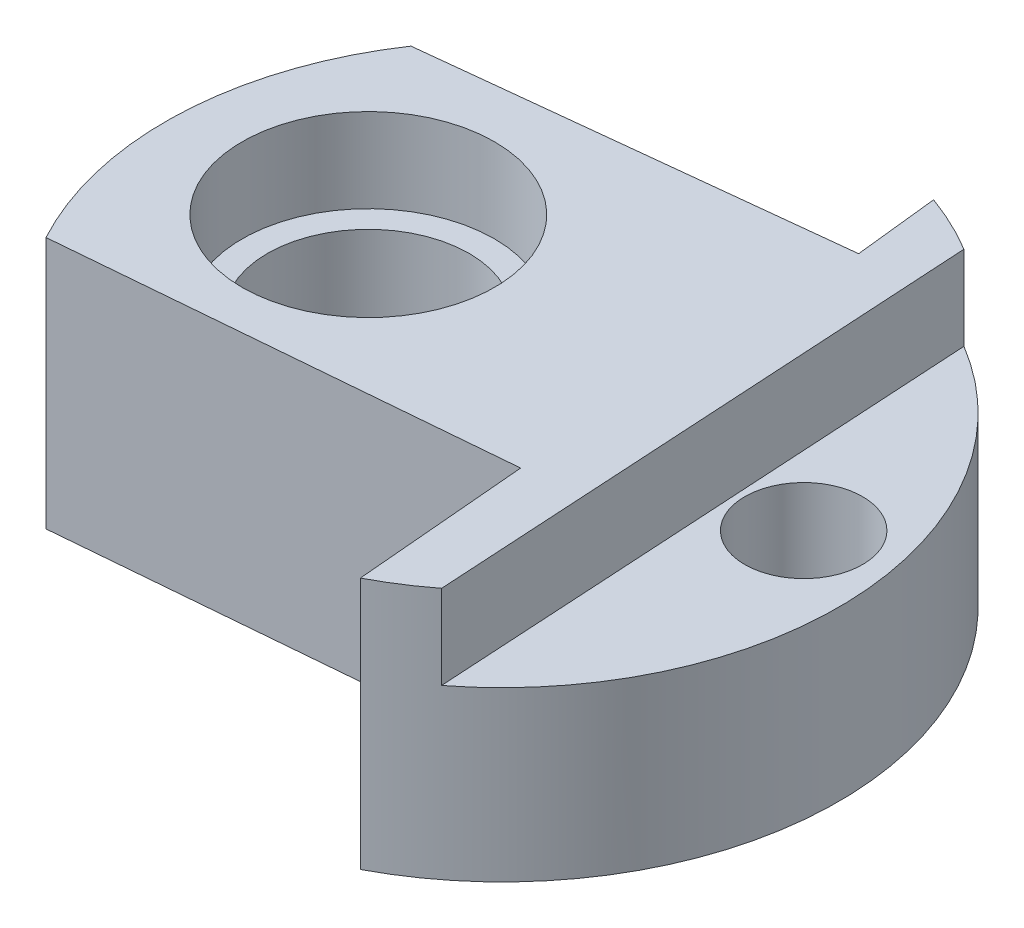
SolidWorks part; units mm, degrees
ref_plane "Front Plane" through (0, 0, 0) normal (0, 0, 1) x (1, 0, 0)
ref_plane "Top Plane" through (0, 0, 0) normal (0, 1, 0) x (1, 0, 0)
ref_plane "Right Plane" through (0, 0, 0) normal (1, 0, 0) x (0, 0, -1)
sketch "Sketch1" plane through (0, 0, 0) normal (0, 1, 0) x (1, 0, 0)
  circle A0 centre (0, 0) radius 20
  dimension "D1" = 40
extrude "Boss-Extrude1" add sketch "Sketch1" along normal blind 15
sketch "Sketch2" plane through (0, 15, 0) normal (0, 1, 0) x (1, 0, 0)
  line L0 (10.2938, 17.1475) -> (12.2252, -15.8286)
  circle A0 centre (0, 0) radius 20 construction
extrude "Cut-Extrude1" cut sketch "Sketch2" against normal blind 5 and the other way through all
sketch "Sketch3" plane through (0, 10, 0) normal (0, 1, 0) x (1, 0, 0)
  circle A0 centre (15.0143, 2.9027) radius 3.5
  dimension "D1" = 7
extrude "Cut-Extrude2" cut sketch "Sketch3" against normal through all
sketch "Sketch4" plane through (0, 15, 0) normal (0, 1, 0) x (1, 0, 0)
  circle A0 centre (-9.1883, 1.2301) radius 6
  dimension "D1" = 12
sketch "Sketch5" plane through (0, 15, 0) normal (0, 1, 0) x (1, 0, 0)
  circle A0 centre (-9.1883, 1.2301) radius 7.5
  dimension "D1" = 15
extrude "Cut-Extrude4" cut sketch "Sketch5" against normal blind 5
extrude "Cut-Extrude5" cut sketch "Sketch4" against normal through all contours A0
sketch "Sketch6" plane through (0, 15, 0) normal (0, 1, 0) x (1, 0, 0)
  line L0 (-17.5847, -9.5278) -> (8.3849, -7.2884)
  line L1 (8.3849, -7.2884) -> (9.284, -17.7146)
  arc A0 (10.2938, 17.1475) -> (12.2252, -15.8286) centre (0, 0) ccw construction
extrude "Cut-Extrude6" cut sketch "Sketch6" against normal through all and the other way through all flip side to cut
sketch "Sketch7" plane through (0, 15, 0) normal (0, 1, 0) x (1, 0, 0)
  line L0 (-16.5916, 11.1678) -> (7.396, 13.7869)
  line L1 (7.396, 13.7869) -> (6.8497, 18.7905)
  arc A0 (10.2938, 17.1475) -> (-17.5847, -9.5278) centre (0, 0) ccw construction
extrude "Cut-Extrude7" cut sketch "Sketch7" against normal through all and the other way through all
